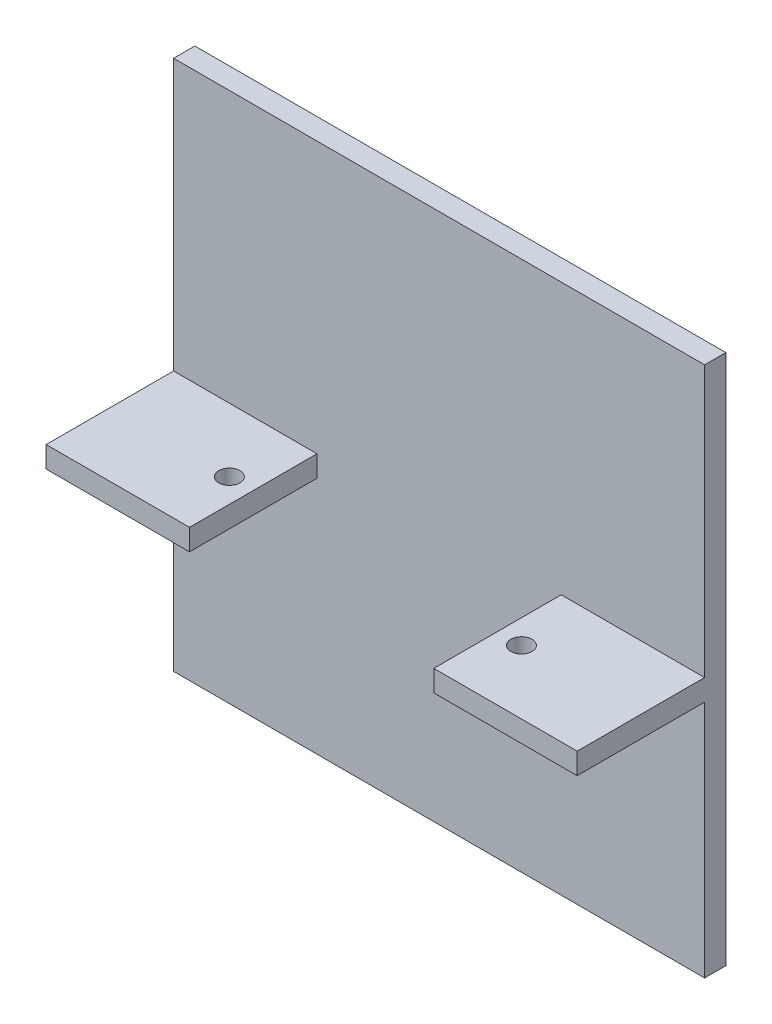
SolidWorks part; units mm, degrees
ref_plane "前视基准面" through (0, 0, 0) normal (0, 0, 1) x (1, 0, 0)
ref_plane "上视基准面" through (0, 0, 0) normal (0, 1, 0) x (1, 0, 0)
ref_plane "右视基准面" through (0, 0, 0) normal (1, 0, 0) x (0, 0, -1)
sketch "草图1" plane through (0, 0, 0) normal (0, 0, 1) x (1, 0, 0)
  line L1 (-25, 25) -> (25, 25)
  line L2 (-25, 25) -> (-25, -25)
  line L3 (-25, -25) -> (25, -25)
  line L4 (25, 25) -> (25, -25)
  line L5 (-25, 25) -> (25, -25) construction
  line L6 (-25, -25) -> (25, 25) construction
  point P0 (0, 0)
  dimension "D1" = 50
  dimension "D2" = 50
extrude "凸台-拉伸1" add sketch "草图1" along normal blind 2
sketch "草图3" plane through (0, -25, 0) normal (0, -1, 0) x (1, 0, 0)
  line L1 (-25, 2) -> (-11.5, 2)
  line L2 (-25, 2) -> (-25, 14)
  line L3 (-25, 14) -> (-11.5, 14)
  line L4 (-11.5, 2) -> (-11.5, 14)
  circle A0 centre (-13.75, 8) radius 1
  dimension "D3" = 2
  dimension "D4" = 6
  dimension "D1" = 12
  dimension "D2" = 11.5
  dimension "D5" = 2.25
extrude "凸台-拉伸3" add sketch "草图3" against normal blind 2 from offset 22.5 offset against normal yes
mirror "镜向1" about plane through (0, 0, 0) normal (1, 0, 0) of "凸台-拉伸3"
